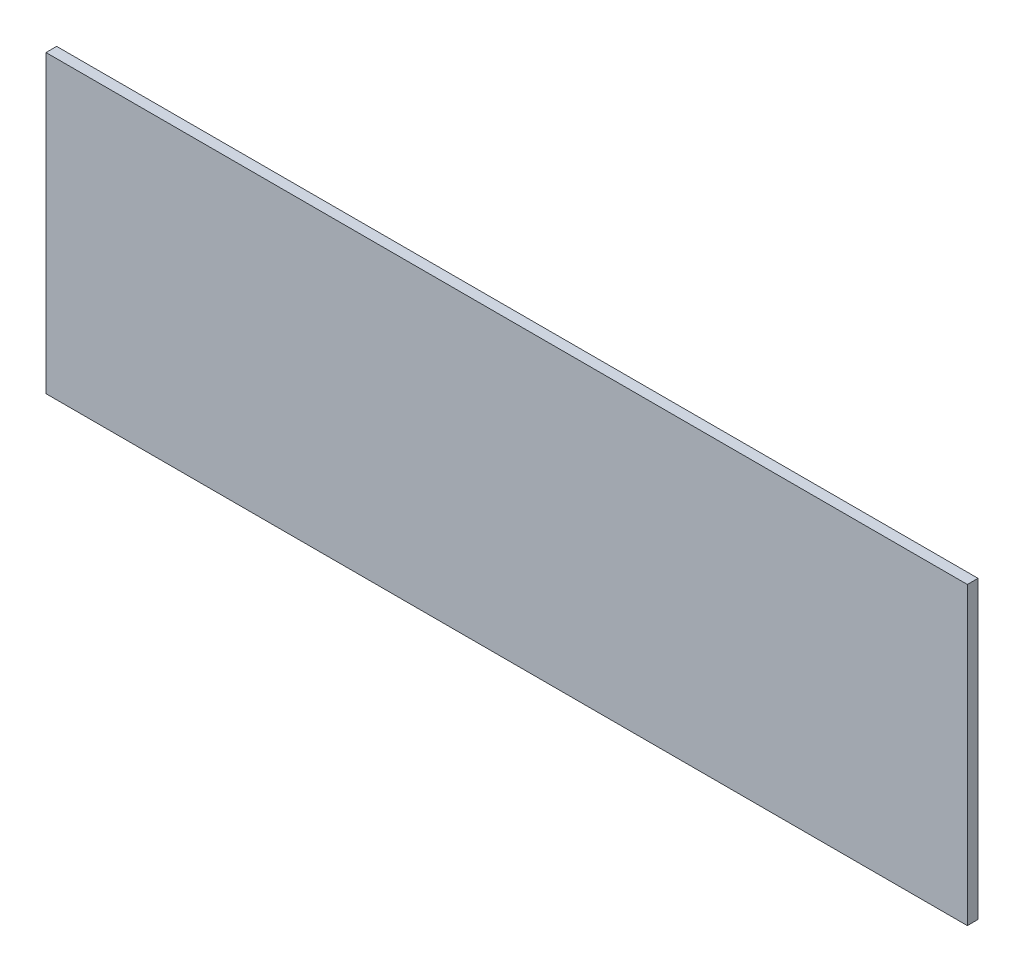
SolidWorks part; units mm, degrees
material "A-Glass Fiber"
ref_plane "Front Plane" through (0, 0, 0) normal (0, 0, 1) x (1, 0, 0)
ref_plane "Top Plane" through (0, 0, 0) normal (0, 1, 0) x (1, 0, 0)
ref_plane "Right Plane" through (0, 0, 0) normal (1, 0, 0) x (0, 0, -1)
sketch "Sketch1" plane through (0, 0, 0) normal (0, 0, 1) x (1, 0, 0)
  line L0 (831.1767, 276.8092) -> (1090.5748, 276.8092) construction
  line L1 (1090.5748, 276.8092) -> (1090.5748, 360) construction
  line L2 (1090.5748, 360) -> (831.1767, 360) construction
  line L3 (831.1767, 360) -> (831.1767, 276.8092) construction
  line L4 (831.1767, 276.8092) -> (1090.5748, 276.8092)
  line L5 (1090.5748, 276.8092) -> (1090.5748, 360)
  line L6 (1090.5748, 360) -> (831.1767, 360)
  line L7 (831.1767, 360) -> (831.1767, 276.8092)
extrude "Boss-Extrude1" add sketch "Sketch1" against normal blind 3
